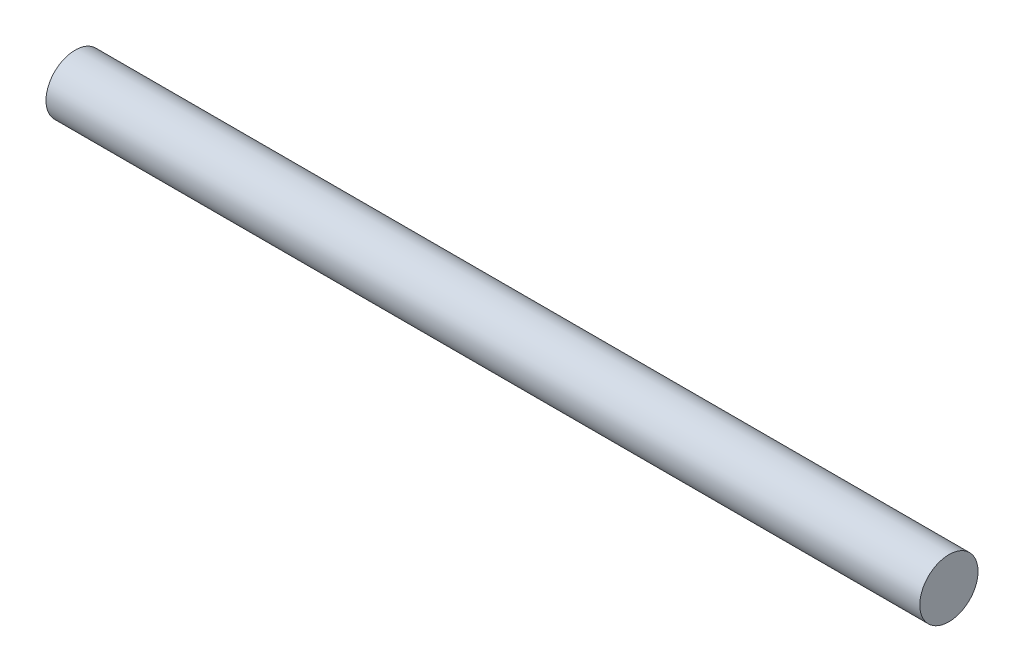
SolidWorks part; units mm, degrees
ref_plane "Front Plane" through (0, 0, 0) normal (0, 0, 1) x (1, 0, 0)
ref_plane "Top Plane" through (0, 0, 0) normal (0, 1, 0) x (1, 0, 0)
ref_plane "Right Plane" through (0, 0, 0) normal (1, 0, 0) x (0, 0, -1)
sketch "Sketch1" plane through (0, 0, 0) normal (0, 0, 1) x (1, 0, 0)
  line L0 (0, 0) -> (11.5789, 0) construction
  line L1 (0, 0) -> (0, 1.5)
  line L2 (0, 1.5) -> (45, 1.5)
  line L3 (45, 1.5) -> (45, 0)
  line L4 (45, 0) -> (0, 0)
  point P3 (45, 0.75)
  dimension "D1" = 3
  dimension "D2" = 45
revolve "Revolve1" add sketch "Sketch1" angle 360 about L0
